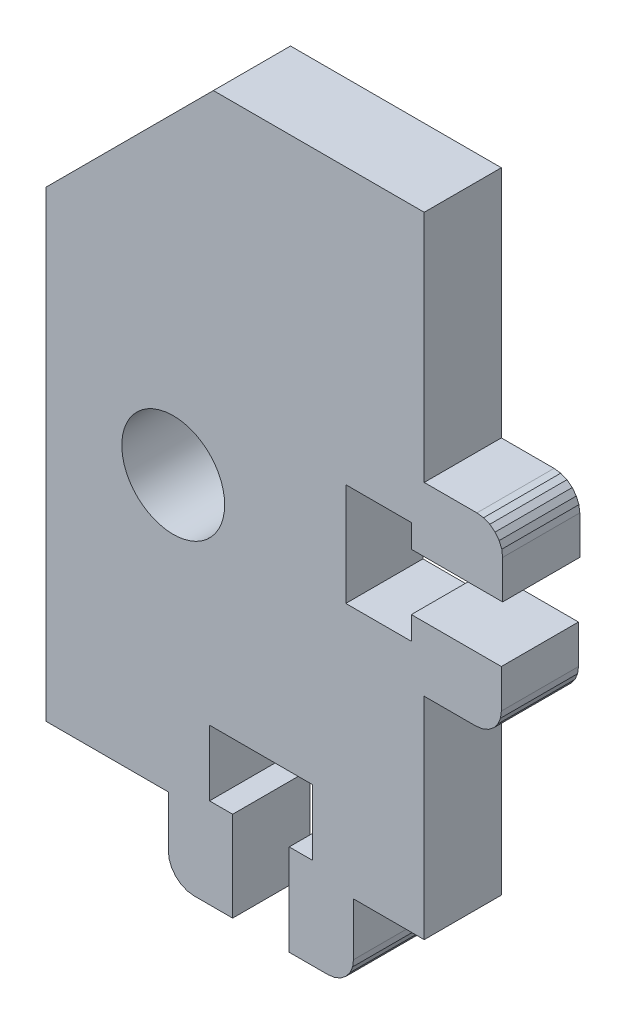
SolidWorks part; units mm, degrees
ref_plane "Plano frontal" through (0, 0, 0) normal (0, 0, 1) x (1, 0, 0)
ref_plane "Plano superior" through (0, 0, 0) normal (0, 1, 0) x (1, 0, 0)
ref_plane "Plano direito" through (0, 0, 0) normal (1, 0, 0) x (0, 0, -1)
sketch "Model" plane through (0, 0, 0) normal (0, 0, 1) x (1, 0, 0)
  line L0 (52.3812, 33.3339) -> (57.4812, 33.3339)
  line L1 (64.4812, 35.1339) -> (64.4812, 32.1339)
  line L2 (58.4812, 13.7339) -> (58.4812, 30.1339)
  line L3 (58.4812, 62.7339) -> (42.0812, 62.7339)
  line L4 (57.4812, 39.5339) -> (64.5812, 39.5339)
  line L5 (57.4812, 35.1339) -> (64.4812, 35.1339)
  line L6 (43.5812, 14.7339) -> (43.5812, 7.7339)
  line L7 (41.7812, 19.8339) -> (41.7812, 14.7339)
  line L8 (38.5812, 13.7339) -> (29.0812, 13.7339)
  line L9 (49.7812, 14.7339) -> (47.9812, 14.7339)
  line L10 (43.5812, 14.7339) -> (41.7812, 14.7339)
  line L11 (57.4812, 41.3339) -> (52.3812, 41.3339)
  line L12 (47.9812, 14.7339) -> (47.9812, 7.6339)
  line L13 (43.5812, 7.7339) -> (40.5812, 7.7339)
  line L14 (49.7812, 14.7339) -> (49.7812, 19.8339)
  line L15 (47.9812, 7.6339) -> (50.9812, 7.6339)
  line L16 (64.5812, 39.5339) -> (64.5812, 42.5339)
  line L17 (42.0812, 62.7339) -> (29.0812, 49.7339)
  line L18 (58.4812, 13.7339) -> (52.9812, 13.7339)
  line L19 (57.4812, 33.3339) -> (57.4812, 35.1339)
  line L20 (58.4812, 44.5339) -> (58.4812, 62.7339)
  line L21 (57.4812, 39.5339) -> (57.4812, 41.3339)
  line L22 (62.5812, 44.5339) -> (58.4812, 44.5339)
  line L23 (62.5812, 44.5339) -> (63.0988, 44.4658)
  line L24 (63.0988, 44.4658) -> (63.5812, 44.266)
  line L25 (63.5812, 44.266) -> (63.9954, 43.9481)
  line L26 (63.9954, 43.9481) -> (64.3132, 43.5339)
  line L27 (64.3132, 43.5339) -> (64.513, 43.0515)
  line L28 (64.513, 43.0515) -> (64.5812, 42.5339)
  line L29 (64.4812, 32.1339) -> (64.413, 31.6163)
  line L30 (64.413, 31.6163) -> (64.2132, 31.1339)
  line L31 (64.2132, 31.1339) -> (63.8954, 30.7197)
  line L32 (63.8954, 30.7197) -> (63.4812, 30.4019)
  line L33 (63.4812, 30.4019) -> (62.9988, 30.2021)
  line L34 (62.4812, 30.1339) -> (58.4812, 30.1339)
  line L35 (62.9988, 30.2021) -> (62.4812, 30.1339)
  line L36 (38.5812, 9.7339) -> (38.5812, 13.7339)
  line L37 (38.5812, 9.7339) -> (38.6493, 9.2163)
  line L38 (38.6493, 9.2163) -> (38.8491, 8.7339)
  line L39 (38.8491, 8.7339) -> (39.167, 8.3197)
  line L40 (39.167, 8.3197) -> (39.5812, 8.0019)
  line L41 (39.5812, 8.0019) -> (40.0635, 7.8021)
  line L42 (40.0635, 7.8021) -> (40.5812, 7.7339)
  line L43 (51.4988, 7.7021) -> (50.9812, 7.6339)
  line L44 (51.9812, 7.9019) -> (51.4988, 7.7021)
  line L45 (52.3954, 8.2197) -> (51.9812, 7.9019)
  line L46 (52.7132, 8.6339) -> (52.3954, 8.2197)
  line L47 (52.913, 9.1163) -> (52.7132, 8.6339)
  line L48 (52.9812, 9.6339) -> (52.913, 9.1163)
  line L49 (52.9812, 9.6339) -> (52.9812, 13.7339)
  line L50 (29.0812, 13.7339) -> (29.0812, 49.7339)
  line L51 (52.3812, 33.3339) -> (52.3812, 41.3339)
  line L52 (41.7812, 19.8339) -> (49.7812, 19.8339)
  circle A0 centre (38.9584, 35.2739) radius 4
extrude "Ressalto-extrusão1" add sketch "Model" along normal blind 6
